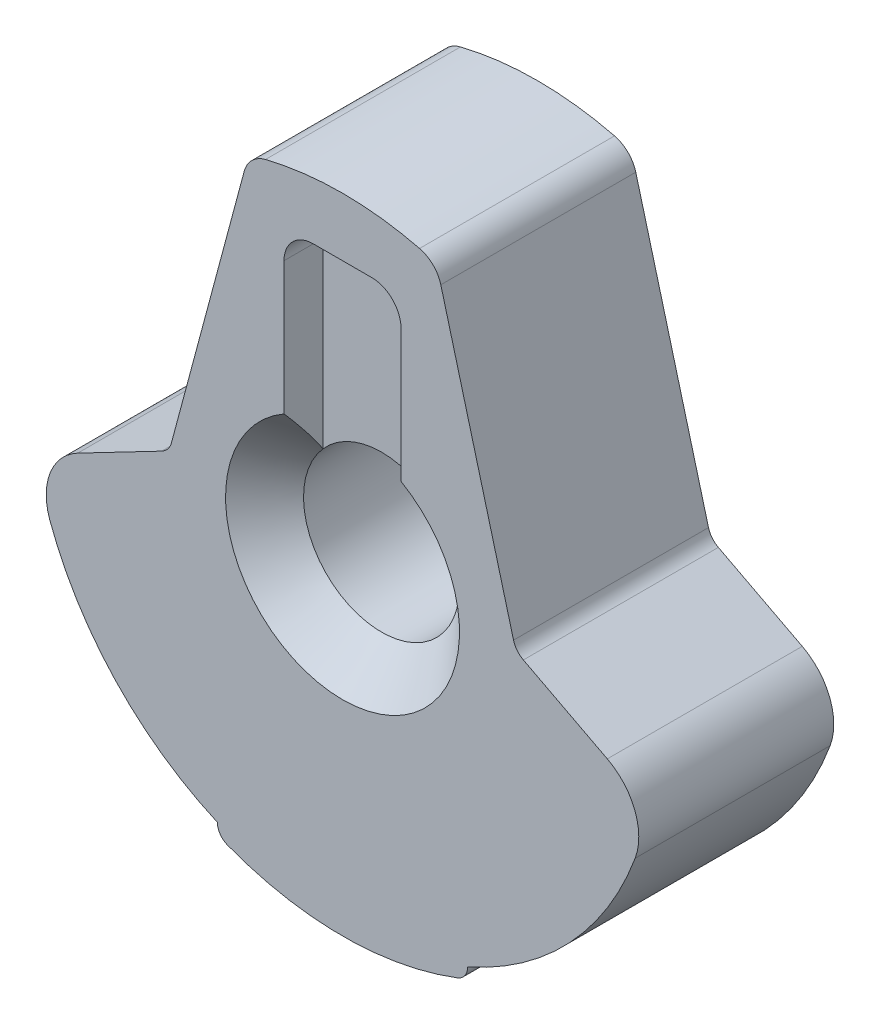
SolidWorks part; units mm, degrees
material "Sinter-Hardened Steel"
ref_plane "Front Plane" through (0, 0, 0) normal (0, 0, 1) x (1, 0, 0)
ref_plane "Top Plane" through (0, 0, 0) normal (0, 1, 0) x (1, 0, 0)
ref_plane "Right Plane" through (0, 0, 0) normal (1, 0, 0) x (0, 0, -1)
sketch "Sketch1" plane through (0, 0, 0) normal (0, 0, 1) x (1, 0, 0)
  line L0 (-5.1903, 0) -> (5.5898, 0) construction
  line L1 (0, -5.1707) -> (0, 5.4096) construction
  line L2 (-2.1385, -0.4079) -> (-2.1385, -3.4559) construction
  line L3 (-2.1385, -0.4079) -> (-4.0435, -0.4079) construction
  line L4 (2.1385, -0.4079) -> (2.1385, -3.4559) construction
  line L5 (2.1385, -0.4079) -> (4.0435, -0.4079) construction
  line L6 (-3.6829, 0.4079) -> (-2.3838, 0.4079)
  line L7 (-2.1385, 0.5961) -> (-1.2806, 3.7977)
  line L8 (1.2806, 3.7977) -> (2.1385, 0.5961)
  line L9 (2.3838, 0.4079) -> (3.6829, 0.4079)
  line L10 (-2.1385, 0.5961) -> (-2.1385, 3.3045) construction
  line L11 (-2.1385, -0.4079) -> (-2.1385, 0) construction
  line L12 (-2.3838, 0.4079) -> (-2.3838, 0) construction
  line L13 (2.1385, 0.5961) -> (2.1385, 2.8696) construction
  line L14 (2.3838, 0) -> (2.3838, 0.4079) construction
  line L15 (2.1385, -0.4079) -> (2.1385, 0) construction
  line L16 (-1.6305, -3.7226) -> (1.6305, -3.7226) construction
  arc A0 (-4.0639, 0.0296) -> (-1.6305, -3.7226) centre (0, 0) ccw
  arc A1 (-2.3838, 0.4079) -> (-2.1385, 0.5961) centre (-2.3838, 0.6619) ccw
  arc A2 (2.1385, 0.5961) -> (2.3838, 0.4079) centre (2.3838, 0.6619) ccw
  arc A3 (1.0039, 4.069) -> (-1.0039, 4.069) centre (0, 0) ccw
  arc A4 (-3.6829, 0.4079) -> (-4.0639, 0.0296) centre (-3.6829, 0.0269) ccw
  arc A5 (-1.2806, 3.7977) -> (-1.0039, 4.069) centre (-0.9126, 3.6991) cw
  arc A6 (1.2806, 3.7977) -> (1.0039, 4.069) centre (0.9126, 3.6991) ccw
  arc A7 (3.6829, 0.4079) -> (4.0639, 0.0296) centre (3.6829, 0.0269) cw
  arc A8 (-1.499, -3.9138) -> (1.499, -3.9138) centre (0, 0) ccw
  arc A9 (-1.499, -3.9138) -> (-1.6305, -3.7226) centre (-1.4258, -3.7226) cw
  arc A10 (1.499, -3.9138) -> (1.6305, -3.7226) centre (1.4258, -3.7226) ccw
  arc A11 (1.6305, -3.7226) -> (4.0639, 0.0296) centre (0, 0) ccw
  point P34 (1.4404, 3.8002)
  dimension "D1" = 8.128
  dimension "D6" = 0.254
  dimension "D7" = 0.254
  dimension "D10" = 0.381
  dimension "D11" = 4.191
  dimension "D13" = 4.191
  dimension "D2" = 3.048
  dimension "D3" = 1.905
  dimension "D4" = 3.048
  dimension "D5" = 1.905
  dimension "D8" = 15
  dimension "D9" = 15
  dimension "D12" = 0.508
extrude "Extrude1" add sketch "Sketch1" along normal blind 2.54
sketch "Sketch2" plane through (0, 0, 2.54) normal (0, 0, 1) x (1, 0, 0)
  line L0 (-2.3838, 0.4079) -> (-3.6829, 0.4079) construction
  line L1 (-2.3838, 0.4079) -> (-3.6829, 0.4079)
  line L2 (-3.9941, -0.7504) -> (-2.3561, 0.1023)
  line L3 (-2.3561, 0.1023) -> (-2.257, 0.1539) construction
  line L4 (-1.2806, 3.7977) -> (-2.1385, 0.5961) construction
  line L5 (-2.2281, 0.2618) -> (-2.1385, 0.5961)
  line L6 (0, 0) -> (0, -3.5831) construction
  arc A0 (-3.6829, 0.4079) -> (-4.0639, 0.0296) centre (-3.6829, 0.0269) ccw construction
  arc A1 (-3.6829, 0.4079) -> (-4.0639, 0.0296) centre (-3.6829, 0.0269) ccw
  arc A2 (-4.0639, 0.0296) -> (-1.6305, -3.7226) centre (0, 0) ccw construction
  arc A3 (-2.3561, 0.1023) -> (-2.2281, 0.2618) centre (-2.4734, 0.3276) ccw
  arc A4 (-2.3838, 0.4079) -> (-2.1385, 0.5961) centre (-2.3838, 0.6619) ccw construction
  arc A5 (-2.3838, 0.4079) -> (-2.1385, 0.5961) centre (-2.3838, 0.6619) ccw
  arc A6 (-4.0639, 0.0296) -> (-3.9941, -0.7504) centre (0, 0) ccw
  dimension "D2" = 0.254
  dimension "D1" = 62.5
  dimension "D3" = 0.254
extrude "Extrude2" cut sketch "Sketch2" against normal through all
sketch "Sketch3" plane through (0, 0, 2.54) normal (0, 0, 1) x (1, 0, 0)
  line L0 (3.6829, 0.4079) -> (2.3838, 0.4079) construction
  line L1 (3.6829, 0.4079) -> (2.3838, 0.4079)
  line L2 (2.3561, 0.1023) -> (3.9941, -0.7504)
  line L3 (2.3561, 0.1023) -> (2.257, 0.1539) construction
  line L4 (2.1385, 0.5961) -> (1.2806, 3.7977) construction
  line L5 (2.1385, 0.5961) -> (2.2281, 0.2618)
  line L6 (0, 0) -> (0, -2.9679) construction
  arc A0 (4.0639, 0.0296) -> (3.6829, 0.4079) centre (3.6829, 0.0269) ccw construction
  arc A1 (4.0639, 0.0296) -> (3.6829, 0.4079) centre (3.6829, 0.0269) ccw
  arc A2 (1.6305, -3.7226) -> (4.0639, 0.0296) centre (0, 0) ccw construction
  arc A3 (3.9941, -0.7504) -> (4.0639, 0.0296) centre (0, 0) ccw
  arc A4 (2.3561, 0.1023) -> (2.2281, 0.2618) centre (2.4734, 0.3276) cw
  arc A5 (2.1385, 0.5961) -> (2.3838, 0.4079) centre (2.3838, 0.6619) ccw construction
  arc A6 (2.1385, 0.5961) -> (2.3838, 0.4079) centre (2.3838, 0.6619) ccw
  dimension "D2" = 0.254
  dimension "D1" = 62.5
  dimension "D3" = 0.254
extrude "Extrude3" cut sketch "Sketch3" against normal through all
fillet "Fillet1" radius 0.762 2 edges at (3.9941, -0.7504, 1.27) (-3.9941, -0.7504, 1.27)
sketch "Sketch6" plane through (0, 0, 2.54) normal (0, 0, 1) x (1, 0, 0)
  circle A0 centre (0, 0) radius 1.016
  dimension "D1" = 2.032
extrude "Extrude6" cut sketch "Sketch6" against normal through all
sketch "Sketch11" plane through (0, 0, 0) normal (0, 1, 0) x (1, 0, 0)
  line L0 (0, -2.54) -> (1.524, -2.54)
  line L2 (0.508, -1.524) -> (0.508, -1.016)
  line L3 (-1.499, -2.54) -> (1.499, -2.54) construction
  line L4 (1.524, 0) -> (0, 0)
  line L7 (0.508, -1.016) -> (1.524, 0)
  line L8 (0.508, -1.524) -> (1.524, -2.54)
  line L9 (0, 0) -> (0, -2.54) construction
  line L10 (0, 0) -> (0, -2.54)
  dimension "D1" = 1.524
  dimension "D2" = 45
  dimension "D4" = 45
  dimension "D6" = 0.508
revolve "Cut-Revolve1" cut sketch "Sketch11" angle 360 about L9
sketch "Sketch9" plane through (0, 0, 0) normal (0, 0, -1) x (-1, 0, 0)
  line L0 (0, 0) -> (0, 0.672) construction
  line L1 (-0.381, 3.429) -> (0.381, 3.429)
  line L2 (-0.762, 3.048) -> (-0.762, 0.672)
  line L3 (-0.762, 0.672) -> (0.762, 0.672)
  line L4 (0.762, 3.048) -> (0.762, 0.672)
  arc A1 (-0.381, 3.429) -> (-0.762, 3.048) centre (-0.381, 3.048) ccw
  arc A2 (0.762, 3.048) -> (0.381, 3.429) centre (0.381, 3.048) ccw
  circle A3 centre (0, 0) radius 1.016 construction
  point P7 (0, 0.672)
  dimension "D3" = 0.381
  dimension "D1" = 1.524
  dimension "D2" = 3.429
extrude "Extrude9" cut sketch "Sketch9" against normal blind 0.508
sketch "Sketch10" plane through (0, 0, 2.54) normal (0, 0, 1) x (1, 0, 0)
  line L0 (0, 0) -> (0, 0.672) construction
  line L1 (-0.381, 3.429) -> (0.381, 3.429)
  line L2 (-0.762, 3.048) -> (-0.762, 0.672)
  line L3 (-0.762, 0.672) -> (0.762, 0.672)
  line L4 (0.762, 3.048) -> (0.762, 0.672)
  arc A1 (-0.762, 3.048) -> (-0.381, 3.429) centre (-0.381, 3.048) cw
  arc A2 (0.381, 3.429) -> (0.762, 3.048) centre (0.381, 3.048) cw
  arc A3 (-0.762, 0.672) -> (0.762, 0.672) centre (0, 0) ccw construction
  dimension "D3" = 0.381
  dimension "D4" = 0.381
  dimension "D1" = 1.524
  dimension "D2" = 3.429
extrude "Extrude10" cut sketch "Sketch10" against normal blind 0.508
